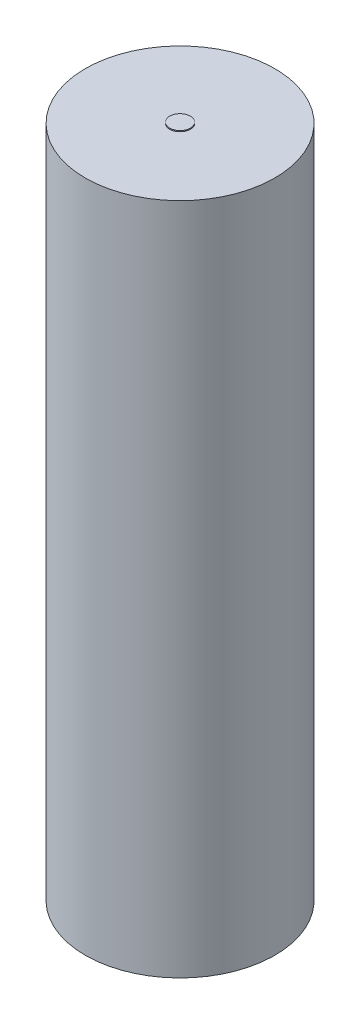
SolidWorks part; units mm, degrees
material "Galvanized Steel"
ref_plane "Front Plane" through (0, 0, 0) normal (0, 0, 1) x (1, 0, 0)
ref_plane "Top Plane" through (0, 0, 0) normal (0, 1, 0) x (1, 0, 0)
ref_plane "Right Plane" through (0, 0, 0) normal (1, 0, 0) x (0, 0, -1)
sketch "Sketch1" plane through (0, 0, 0) normal (0, 1, 0) x (1, 0, 0)
  circle A0 centre (0, 0) radius 9.15
  dimension "D1" = 18.3
extrude "Boss-Extrude1" add sketch "Sketch1" against normal blind 65
sketch "Sketch2" plane through (0, 0, 0) normal (0, 1, 0) x (1, 0, 0)
  circle A0 centre (0, 0) radius 1
  dimension "D1" = 2
extrude "Boss-Extrude2" add sketch "Sketch2" along normal blind 0.1
sketch "Sketch3" plane through (0, -65, 0) normal (0, -1, 0) x (1, 0, 0)
  circle A0 centre (0, 0) radius 1
  dimension "D1" = 2
extrude "Boss-Extrude3" add sketch "Sketch3" along normal blind 0.1
